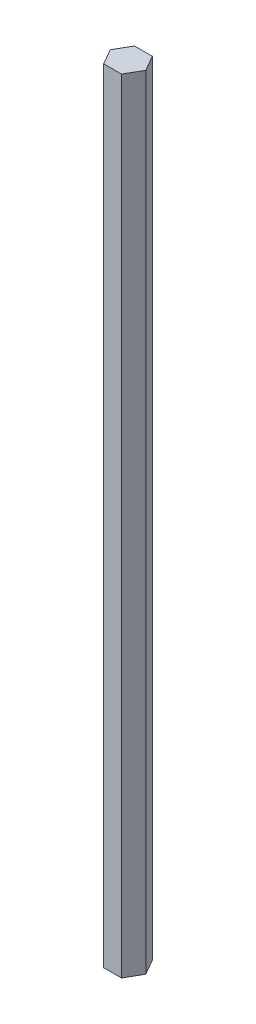
SolidWorks part; units mm, degrees
ref_plane "Front Plane" through (0, 0, 0) normal (0, 0, 1) x (1, 0, 0)
ref_plane "Top Plane" through (0, 0, 0) normal (0, 1, 0) x (1, 0, 0)
ref_plane "Right Plane" through (0, 0, 0) normal (1, 0, 0) x (0, 0, -1)
sketch "Sketch1" plane through (0, 0, 0) normal (0, 1, 0) x (1, 0, 0)
  line L1 (7.9771, 1.5793) -> (3.9771, 8.5075)
  line L2 (3.9771, 8.5075) -> (-4.0229, 8.5075)
  line L3 (-4.0229, 8.5075) -> (-8.0229, 1.5793)
  line L4 (-8.0229, 1.5793) -> (-4.0229, -5.3489)
  line L5 (-4.0229, -5.3489) -> (3.9771, -5.3489)
  line L6 (3.9771, -5.3489) -> (7.9771, 1.5793)
  circle A0 centre (-0.0229, 1.5793) radius 6.9282 construction
  dimension "D1" = 8
extrude "Boss-Extrude1" add sketch "Sketch1" along normal blind 352
